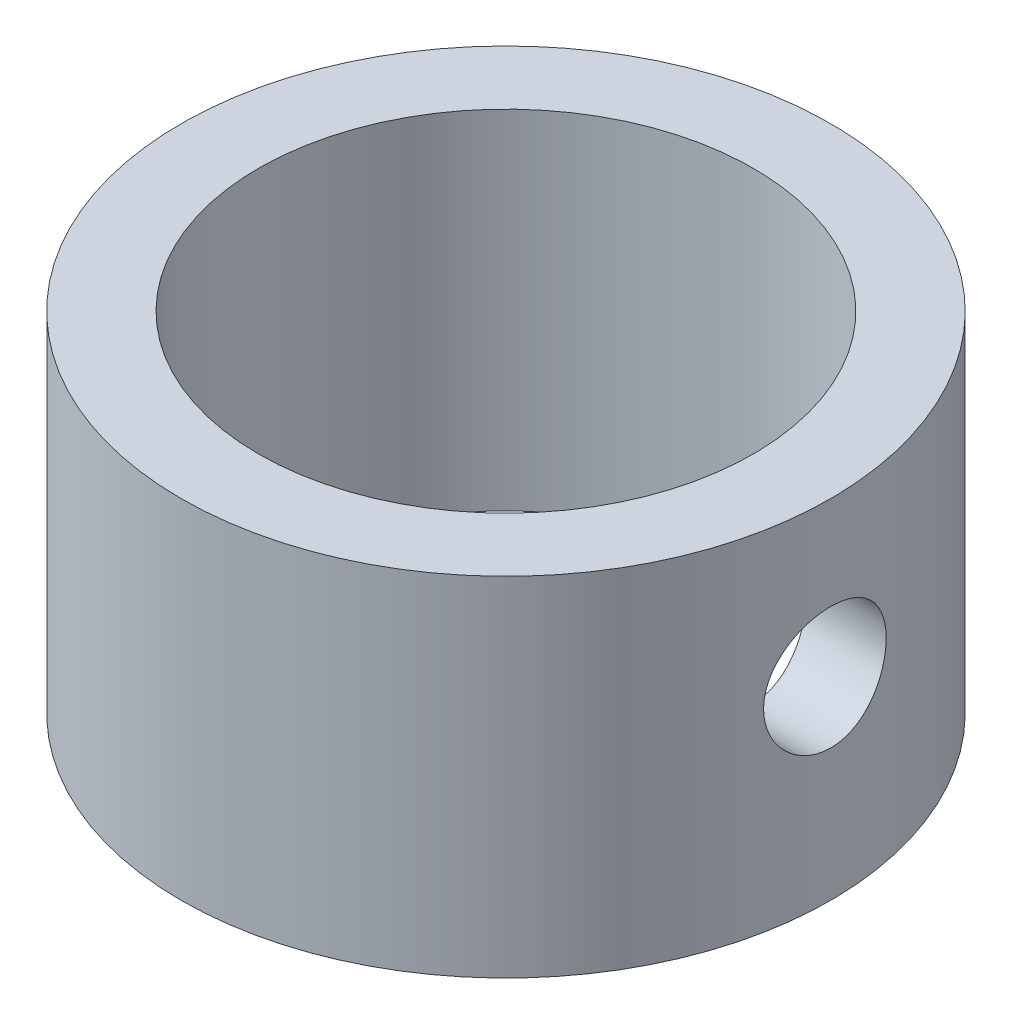
SolidWorks part; units mm, degrees
ref_plane "Front Plane" through (0, 0, 0) normal (0, 0, 1) x (1, 0, 0)
ref_plane "Top Plane" through (0, 0, 0) normal (0, 1, 0) x (1, 0, 0)
ref_plane "Right Plane" through (0, 0, 0) normal (1, 0, 0) x (0, 0, -1)
sketch "Sketch1" plane through (0, 0, 0) normal (0, 1, 0) x (1, 0, 0)
  circle A0 centre (0, 0) radius 1.6
  circle A1 centre (0, 0) radius 2.1
  dimension "D1" = 3.2
  dimension "D2" = 0.5
extrude "Boss-Extrude1" add sketch "Sketch1" along normal blind 1 and the other way blind 1.25
ref_plane "Plane1" through (2.1, 0, 0) normal (1, 0, 0) x (0, 0, -1)
hole_wizard "Tap Drill for 100 UNM Tap9" positions "3DSketch1" profile "Sketch8" hole size "100 UNM" standard "Superior"
sketch3d "3DSketch1"
  point P0 (2.1, 0, 0)
  point P6 (0, 0, 0)
  point P10 (0, 0, 0)
  point P11 (1.125, -0.6594, 0)
  dimension "D1" = 0
  dimension "D2" = 0
sketch "Sketch8" plane through (2.1, 0, 0) normal (0, 1, 0) x (0, 0, -1)
  line L0 (0, 0) -> (0, 0.5)
  line L1 (0, 0.5) -> (0.3962, 0.5)
  line L2 (0.3962, 0.5) -> (0.3962, 0)
  line L5 (0.3962, 0) -> (0, 0)
  line L11 (0, -6.35) -> (0, 107.95) construction
  dimension "Thru Hole Dia." = 0.7925
  dimension "Thru Hole Depth" = 0.5
